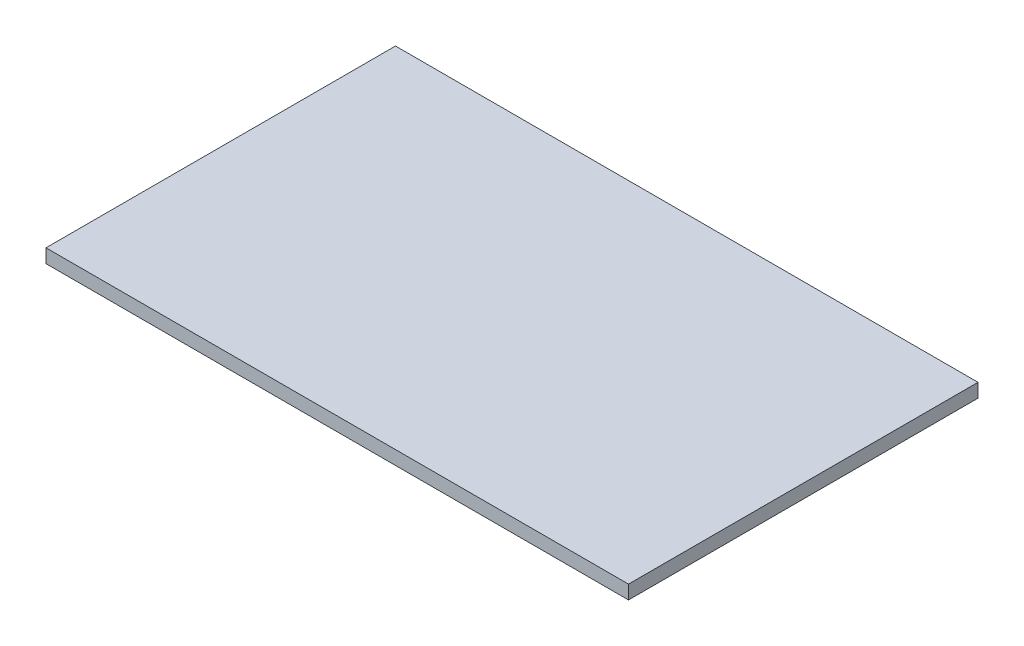
SolidWorks part; units mm, degrees
ref_plane "Front Plane" through (0, 0, 0) normal (0, 0, 1) x (1, 0, 0)
ref_plane "Top Plane" through (0, 0, 0) normal (0, 1, 0) x (1, 0, 0)
ref_plane "Right Plane" through (0, 0, 0) normal (1, 0, 0) x (0, 0, -1)
sketch "Sketch1" plane through (0, 0, 0) normal (0, 1, 0) x (1, 0, 0)
  line L1 (-127, 76.2) -> (127, 76.2)
  line L2 (-127, 76.2) -> (-127, -76.2)
  line L3 (-127, -76.2) -> (127, -76.2)
  line L4 (127, 76.2) -> (127, -76.2)
  line L5 (-127, 76.2) -> (127, -76.2) construction
  line L6 (-127, -76.2) -> (127, 76.2) construction
  point P0 (0, 0)
extrude "Boss-Extrude1" add sketch "Sketch1" along normal blind 6 contours L1 L4 L3 L2
